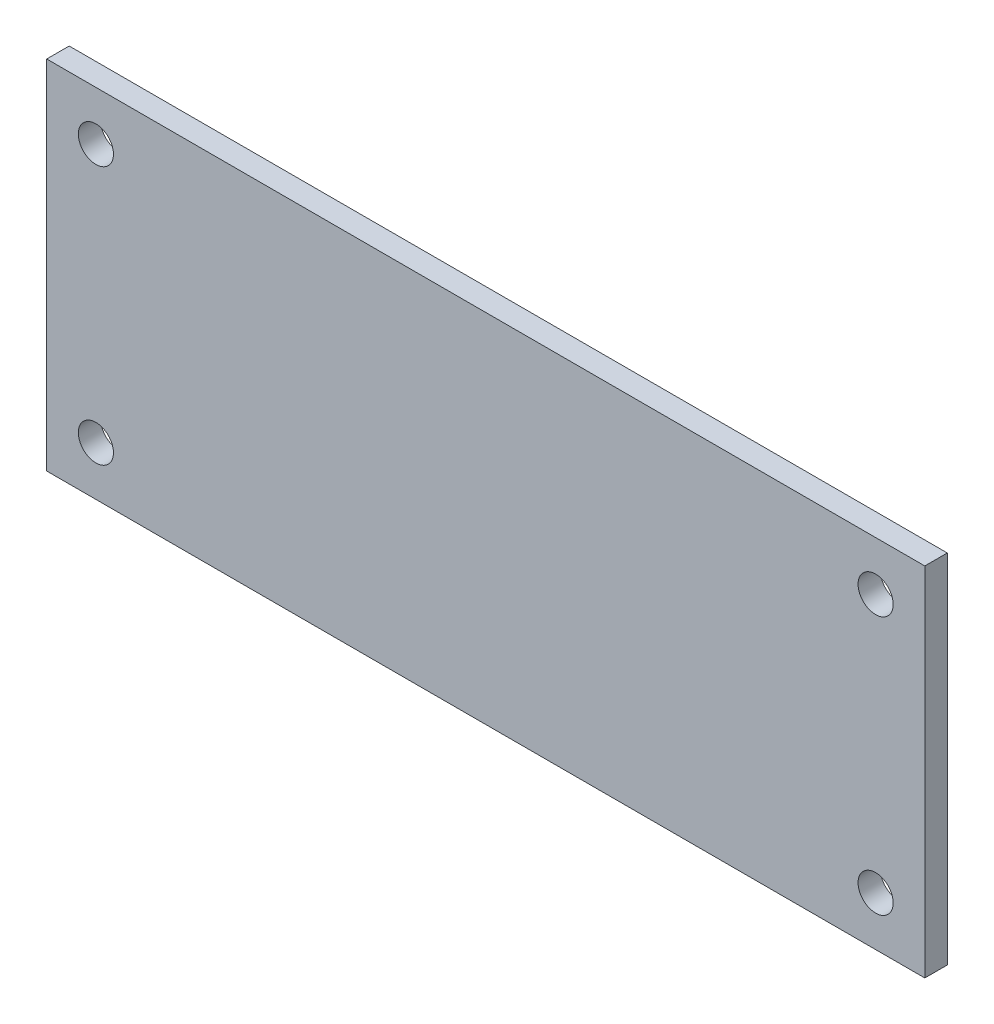
SolidWorks part; units mm, degrees
ref_plane "Front Plane" through (0, 0, 0) normal (0, 0, 1) x (1, 0, 0)
ref_plane "Top Plane" through (0, 0, 0) normal (0, 1, 0) x (1, 0, 0)
ref_plane "Right Plane" through (0, 0, 0) normal (1, 0, 0) x (0, 0, -1)
sketch "Sketch1" plane through (0, 0, 0) normal (0, 0, 1) x (1, 0, 0)
  line L1 (-31.25, -12.7) -> (31.25, -12.7)
  line L2 (-31.25, -12.7) -> (-31.25, 12.7)
  line L3 (-31.25, 12.7) -> (31.25, 12.7)
  line L4 (31.25, -12.7) -> (31.25, 12.7)
  line L5 (-31.25, -12.7) -> (31.25, 12.7) construction
  line L6 (-31.25, 12.7) -> (31.25, -12.7) construction
  circle A0 centre (-27.75, 9.2) radius 1.25
  circle A1 centre (27.75, 9.2) radius 1.25
  circle A2 centre (27.75, -9.2) radius 1.25
  circle A3 centre (-27.75, -9.2) radius 1.25
  point P0 (0, 0)
  point P14 (0, 0)
  point P15 (0, 0)
  point P16 (-31.25, 9.5463)
  point P17 (0, 0)
  point P18 (0, 0)
  dimension "D5" = 2.5
  dimension "D1" = 25.4
  dimension "D2" = 62.5
  dimension "D3" = 3.5
  dimension "D4" = 3.5
  dimension "D6" = 3.5
  dimension "D7" = 3.5
  dimension "D8" = 55.5
  dimension "D9" = 18.4
extrude "Boss-Extrude1" add sketch "Sketch1" along normal blind 1.6
